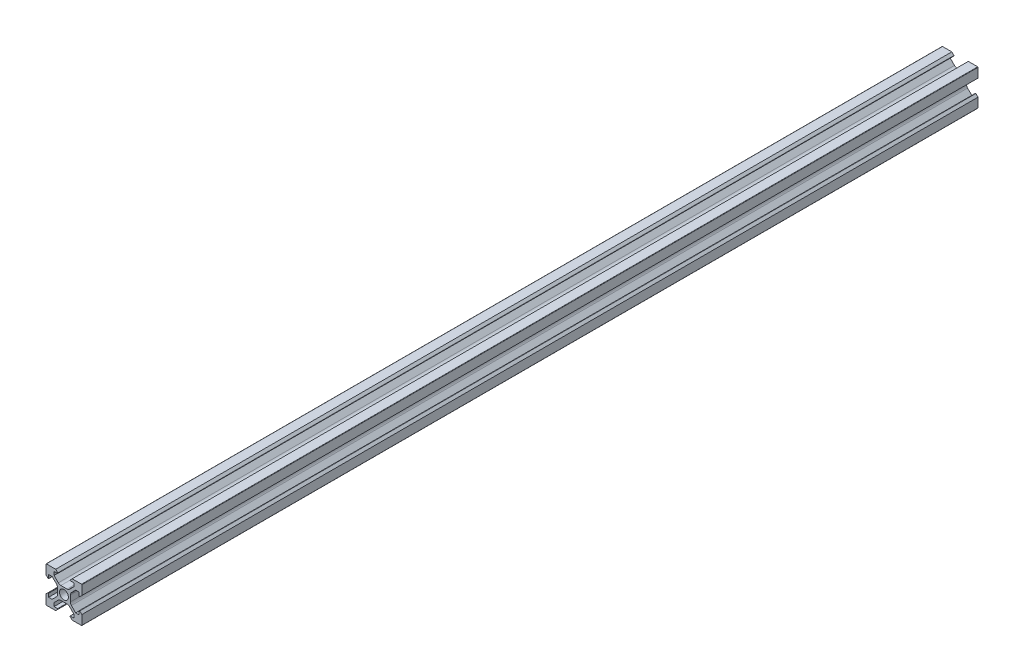
SolidWorks part; units mm, degrees
material "Liga 1350"
ref_plane "Plano frontal" through (0, 0, 0) normal (0, 0, 1) x (1, 0, 0)
ref_plane "Plano superior" through (0, 0, 0) normal (0, 1, 0) x (1, 0, 0)
ref_plane "Plano direito" through (0, 0, 0) normal (1, 0, 0) x (0, 0, -1)
sketch "Esboço1" plane through (0, 0, 0) normal (0, 0, 1) x (1, 0, 0)
  line L0 (0, 13.8681) -> (0, -15.879) construction
  line L1 (-4.6, -10) -> (-9.8, -10)
  line L2 (-3.4414, -8.8414) -> (-4.6, -10)
  line L3 (-4.1858, -3.1251) -> (-6.5607, -5.5)
  line L4 (-10, 9.8) -> (-10, 4.6)
  line L5 (-5.5, -8.5) -> (-3.5828, -8.5)
  line L6 (-5.5, -8.5) -> (-5.5, -6.5607)
  line L7 (-8.5, -5.5) -> (-8.5, -3.5828)
  line L8 (-21.5514, 0) -> (2.5, 0) construction
  line L9 (-3.1251, 4.1858) -> (-5.5, 6.5607)
  line L10 (-8.8414, -3.4414) -> (-10, -4.6)
  line L11 (-8.5, 5.5) -> (-6.5607, 5.5)
  line L12 (-8.8414, 3.4414) -> (-10, 4.6)
  line L13 (-8.5, -5.5) -> (-6.5607, -5.5)
  line L14 (-8.5, 5.5) -> (-8.5, 3.5828)
  line L15 (-3.1251, -4.1858) -> (-5.5, -6.5607)
  line L16 (-21.5514, 0) -> (20.6623, 0) construction
  line L17 (-8.5, 10) -> (-8.5, -10) construction
  line L18 (-10, -9.8) -> (-10, -4.6)
  line L19 (-21.5514, 5.5) -> (20.6623, 5.5) construction
  line L21 (-10, 10) -> (-10, -10) construction
  line L22 (3.6, 1.7109) -> (3.6, 0) construction
  line L23 (21.5514, 0) -> (-2.5, 0) construction
  line L24 (4.6, 10) -> (9.8, 10)
  line L25 (-5.5, 8.5) -> (-5.5, 6.5607)
  line L26 (3.4414, 8.8414) -> (4.6, 10)
  line L27 (-5.5, 8.5) -> (-3.5828, 8.5)
  line L28 (4.1858, 3.1251) -> (6.5607, 5.5)
  line L29 (5.5, 8.5) -> (3.5828, 8.5)
  line L30 (5.5, 8.5) -> (5.5, 6.5607)
  line L31 (-3.6, 1.7109) -> (-3.6, -1.7109)
  line L33 (10, -9.8) -> (10, -4.6)
  line L34 (-4.1858, 3.1251) -> (-6.5607, 5.5)
  line L35 (-3.4414, 8.8414) -> (-4.6, 10)
  line L36 (-4.6, 10) -> (-9.8, 10)
  line L37 (3.1251, -4.1858) -> (5.5, -6.5607)
  line L38 (8.5, 5.5) -> (8.5, 3.5828)
  line L39 (8.5, -5.5) -> (6.5607, -5.5)
  line L40 (8.8414, 3.4414) -> (10, 4.6)
  line L41 (8.5, 5.5) -> (6.5607, 5.5)
  line L42 (8.8414, -3.4414) -> (10, -4.6)
  line L43 (3.1251, 4.1858) -> (5.5, 6.5607)
  line L44 (8.5, -5.5) -> (8.5, -3.5828)
  line L45 (5.5, -8.5) -> (5.5, -6.5607)
  line L46 (5.5, -8.5) -> (3.5828, -8.5)
  line L47 (10, 9.8) -> (10, 4.6)
  line L48 (4.1858, -3.1251) -> (6.5607, -5.5)
  line L49 (3.4414, -8.8414) -> (4.6, -10)
  line L50 (4.6, -10) -> (9.8, -10)
  line L51 (-1.7109, 3.6) -> (1.7109, 3.6)
  line L52 (3.6, 1.7109) -> (3.6, -1.7109)
  line L53 (1.7109, -3.6) -> (-1.7109, -3.6)
  circle A0 centre (0, 0) radius 2.5
  arc A1 (-3.6, 1.7109) -> (-4.1858, 3.1251) centre (-5.6, 1.7109) ccw
  arc A2 (-8.5, 3.5828) -> (-8.8414, 3.4414) centre (-8.7, 3.5828) cw
  arc A3 (-9.8, 10) -> (-10, 9.8) centre (-9.8, 9.8) ccw
  arc A4 (-1.7109, 3.6) -> (-3.1251, 4.1858) centre (-1.7109, 5.6) cw
  arc A5 (-3.5828, 8.5) -> (-3.4414, 8.8414) centre (-3.5828, 8.7) ccw
  arc A6 (-3.5828, -8.5) -> (-3.4414, -8.8414) centre (-3.5828, -8.7) cw
  arc A7 (-1.7109, -3.6) -> (-3.1251, -4.1858) centre (-1.7109, -5.6) ccw
  arc A8 (-9.8, -10) -> (-10, -9.8) centre (-9.8, -9.8) cw
  arc A9 (-8.5, -3.5828) -> (-8.8414, -3.4414) centre (-8.7, -3.5828) ccw
  arc A10 (-3.6, -1.7109) -> (-4.1858, -3.1251) centre (-5.6, -1.7109) cw
  arc A11 (3.6, -1.7109) -> (4.1858, -3.1251) centre (5.6, -1.7109) ccw
  arc A12 (8.5, -3.5828) -> (8.8414, -3.4414) centre (8.7, -3.5828) cw
  arc A13 (9.8, -10) -> (10, -9.8) centre (9.8, -9.8) ccw
  arc A14 (1.7109, -3.6) -> (3.1251, -4.1858) centre (1.7109, -5.6) cw
  arc A15 (3.5828, -8.5) -> (3.4414, -8.8414) centre (3.5828, -8.7) ccw
  arc A16 (3.5828, 8.5) -> (3.4414, 8.8414) centre (3.5828, 8.7) cw
  arc A17 (1.7109, 3.6) -> (3.1251, 4.1858) centre (1.7109, 5.6) ccw
  arc A18 (9.8, 10) -> (10, 9.8) centre (9.8, 9.8) cw
  arc A19 (8.5, 3.5828) -> (8.8414, 3.4414) centre (8.7, 3.5828) ccw
  arc A20 (3.6, 1.7109) -> (4.1858, 3.1251) centre (5.6, 1.7109) cw
  point P0 (0, 0)
  point P45 (-3.6, 2.5393)
extrude "Ressalto-extrusão1" add sketch "Esboço1" along normal blind 500
